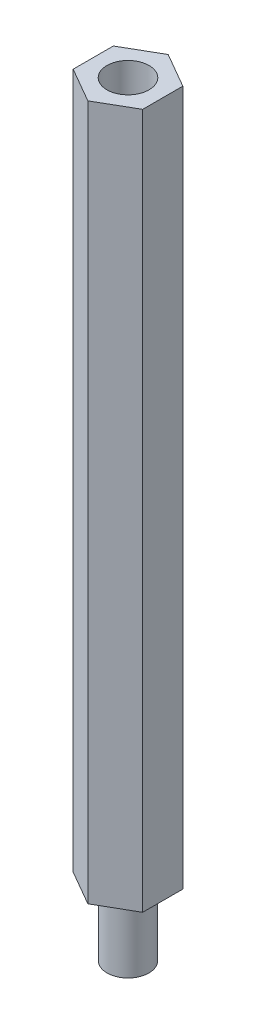
SolidWorks part; units mm, degrees
ref_plane "Front Plane" through (0, 0, 0) normal (0, 0, 1) x (1, 0, 0)
ref_plane "Top Plane" through (0, 0, 0) normal (0, 1, 0) x (1, 0, 0)
ref_plane "Right Plane" through (0, 0, 0) normal (1, 0, 0) x (0, 0, -1)
sketch "Sketch1" plane through (0, 0, 0) normal (0, 1, 0) x (1, 0, 0)
  line L1 (0, -2.8868) -> (2.5, -1.4434)
  line L2 (2.5, -1.4434) -> (2.5, 1.4434)
  line L3 (2.5, 1.4434) -> (0, 2.8868)
  line L4 (0, 2.8868) -> (-2.5, 1.4434)
  line L5 (-2.5, 1.4434) -> (-2.5, -1.4434)
  line L6 (-2.5, -1.4434) -> (0, -2.8868)
  circle A0 centre (0, 0) radius 2.5 construction
extrude "Boss-Extrude1" add sketch "Sketch1" along normal blind 50
sketch "Sketch2" plane through (0, 50, 0) normal (0, 1, 0) x (1, 0, 0)
  circle A0 centre (0, 0) radius 1.5161
extrude "Cut-Extrude1" cut sketch "Sketch2" against normal blind 10
sketch "Sketch3" plane through (0, 0, 0) normal (0, -1, 0) x (1, 0, 0)
  circle A0 centre (0, 0) radius 1.5059
extrude "Boss-Extrude2" add sketch "Sketch3" along normal blind 5
